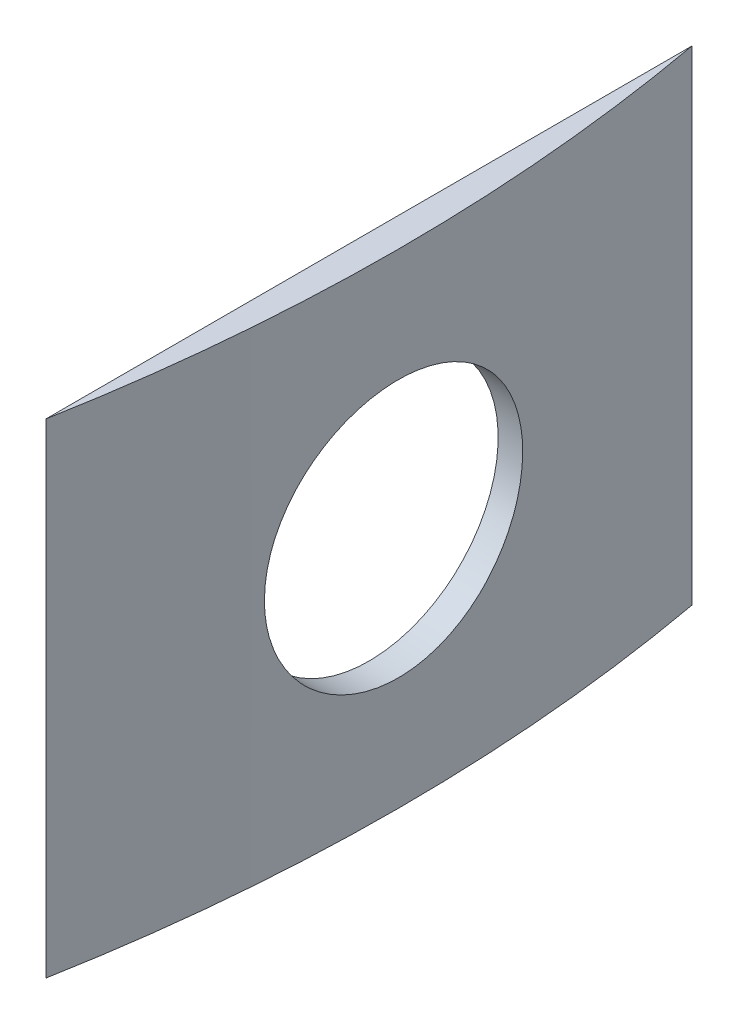
SolidWorks part; units mm, degrees
ref_plane "Front Plane" through (0, 0, 0) normal (0, 0, 1) x (1, 0, 0)
ref_plane "Top Plane" through (0, 0, 0) normal (0, 1, 0) x (1, 0, 0)
ref_plane "Right Plane" through (0, 0, 0) normal (1, 0, 0) x (0, 0, -1)
sketch "Sketch2" plane through (0, 0, 0) normal (0, 1, 0) x (1, 0, 0)
  line L1 (0, 0) -> (54.8458, -10)
  line L6 (0, 0) -> (54.8458, 10)
  line L7 (0, 0) -> (55.75, 0)
  line L8 (54.8458, -10) -> (54.8458, 10)
  line L9 (54.8458, 10) -> (54.2063, 12)
  line L10 (54.2063, 12) -> (54.2063, -12)
  line L11 (54.2063, -12) -> (54.8458, -10)
  circle A0 centre (0, 0) radius 55.75
  circle A1 centre (0, 0) radius 55.5186
  dimension "D1" = 111.5
  dimension "D2" = 20
  dimension "D3" = 90
  dimension "D5" = 24
extrude "Boss-Extrude1" add sketch "Sketch2" along normal blind 15 contours A1 L7 A0 L8 | L7 A1 L8 | L8 A1 L7 | A1 L8 A0 L7
ref_plane "Plane1" through (43.4646, 0, 0) normal (-1, 0, 0) x (0, 0, 1)
sketch "Sketch3" plane through (43.4646, 0, 0) normal (-1, 0, 0) x (0, 0, 1)
  line L0 (0, 0) -> (0, 15)
  line L1 (-12, 15) -> (12, 15) construction
  line L2 (0, 15) -> (12, 7.5)
  line L3 (12, 15) -> (12, 0) construction
  line L4 (12, 7.5) -> (0, 7.5)
  circle A0 centre (0, 7.5) radius 4
  dimension "D1" = 8
extrude "Cut-Extrude1" cut sketch "Sketch3" against normal blind 40 contours L0 A0 | L0 A0 L4 | L4 A0 L0
